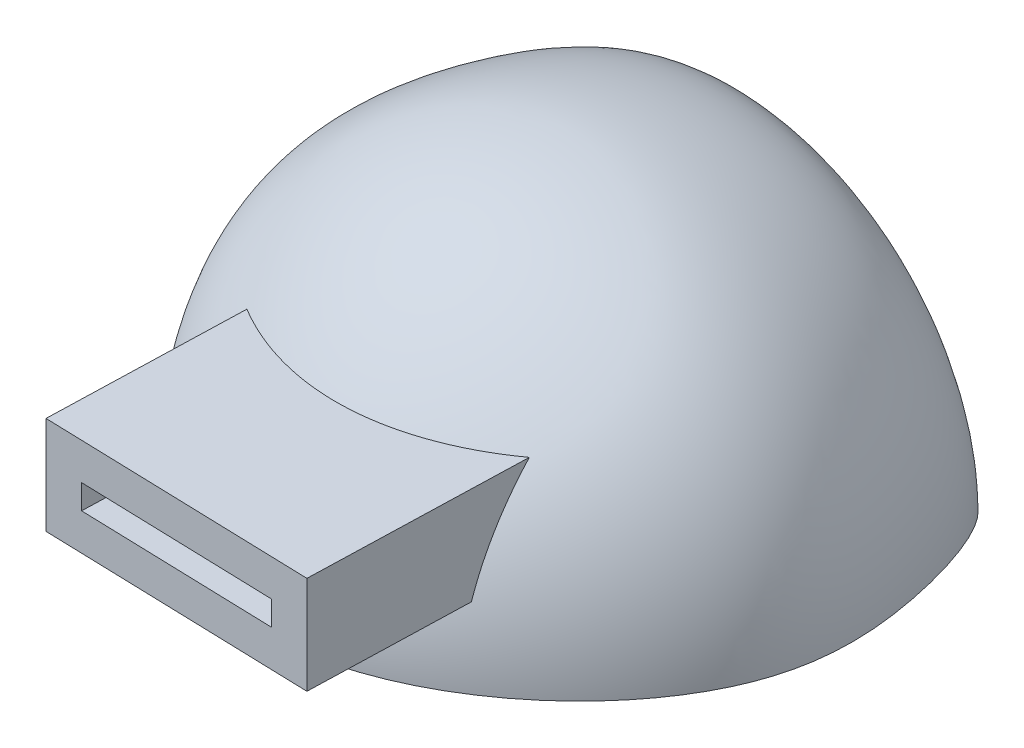
SolidWorks part; units mm, degrees
ref_plane "Front Plane" through (0, 0, 0) normal (0, 0, 1) x (1, 0, 0)
ref_plane "Top Plane" through (0, 0, 0) normal (0, 1, 0) x (1, 0, 0)
ref_plane "Right Plane" through (0, 0, 0) normal (1, 0, 0) x (0, 0, -1)
sketch "Sketch2" plane through (0, 0, 0) normal (0, 1, 0) x (1, 0, 0)
  line L0 (32.4962, -75.7592) -> (32.4962, -102.8306)
  arc A0 (82.058, 7.8703) -> (32.4962, -75.7592) centre (0, 0) cw
  spline S0 degree 3 poles (82.058, 7.8703) (93.0415, 34.1625) (112.3481, -13.7258) (106.2843, -68.6519) (61.355, -101.9668) (32.4962, -102.8306) knots 0 0 0 0 0.267589 0.512712 1 1 1 1
  point P5 (0, 0)
  point P7 (0, 0)
revolve "Revolve1" add sketch "Sketch2" angle 180 about L0
ref_plane "Plane1" through (32.4962, 0, 102.8306) normal (-0.0299, 0, 0.9996) x (0.9996, 0, 0.0299)
sketch "Sketch3" plane through (32.4962, 0, 102.8306) normal (-0.0299, 0, 0.9996) x (0.9996, 0, 0.0299)
  line L1 (-23.6997, 34.8794) -> (27.1003, 34.8794)
  line L2 (-23.6997, 34.8794) -> (-23.6997, 28.5294)
  line L3 (-23.6997, 28.5294) -> (27.1003, 28.5294)
  line L4 (27.1003, 34.8794) -> (27.1003, 28.5294)
  line L5 (-23.6997, 34.8794) -> (27.1003, 28.5294) construction
  line L6 (-23.6997, 28.5294) -> (27.1003, 34.8794) construction
  line L7 (36.6253, 19.0044) -> (-33.2247, 19.0044)
  line L8 (36.6253, 19.0044) -> (36.6253, 44.4044)
  line L9 (36.6253, 44.4044) -> (-33.2247, 44.4044)
  line L10 (-33.2247, 19.0044) -> (-33.2247, 44.4044)
  line L11 (36.6253, 19.0044) -> (-33.2247, 44.4044) construction
  line L12 (36.6253, 44.4044) -> (-33.2247, 19.0044) construction
  point P0 (1.7003, 31.7044)
  point P5 (1.7003, 31.7044)
  dimension "D1" = 6.35
  dimension "D2" = 50.8
  dimension "D3" = 31.75
  dimension "D4" = 69.85
  dimension "D5" = 25.4
  dimension "D6" = 34.8794
extrude "Boss-Extrude7" add sketch "Sketch3" along normal blind 25.4 and the other way blind 38.1
